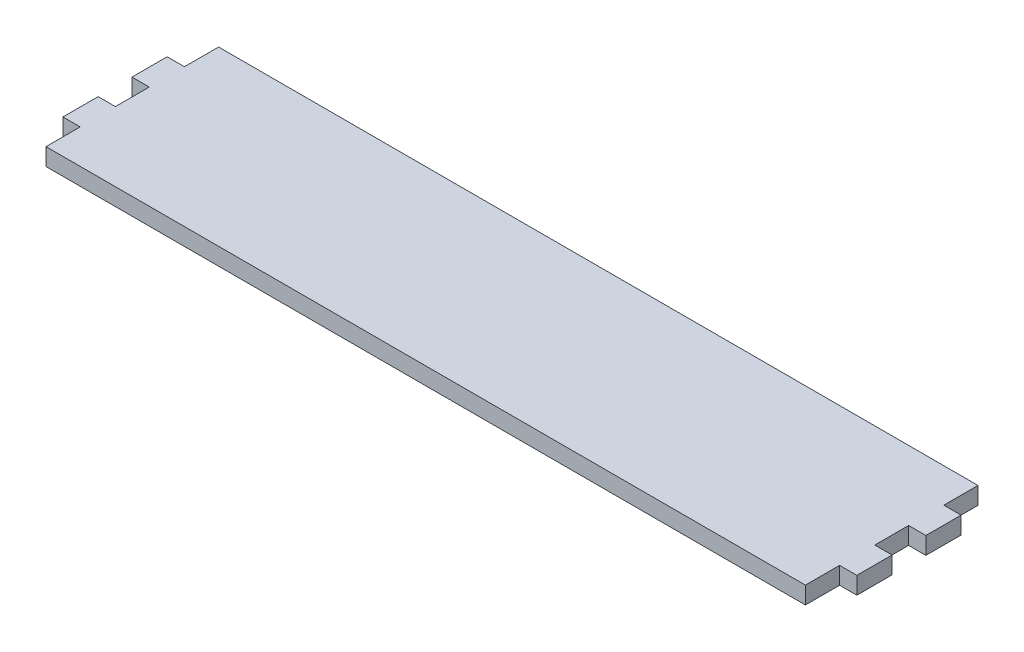
SolidWorks part; units mm, degrees
ref_plane "Front Plane" through (0, 0, 0) normal (0, 0, 1) x (1, 0, 0)
ref_plane "Top Plane" through (0, 0, 0) normal (0, 1, 0) x (1, 0, 0)
ref_plane "Right Plane" through (0, 0, 0) normal (1, 0, 0) x (0, 0, -1)
sketch "Sketch1" plane through (0, 0, 0) normal (0, 1, 0) x (1, 0, 0)
  line L0 (0, 0) -> (279.4, 0)
  line L1 (279.4, 0) -> (279.4, -12.573)
  line L2 (279.4, -12.573) -> (285.75, -12.573)
  line L3 (285.75, -12.573) -> (285.75, -25.527)
  line L4 (285.75, -25.527) -> (279.4, -25.527)
  line L5 (279.4, -25.527) -> (279.4, -37.973)
  line L6 (279.4, -37.973) -> (285.75, -37.973)
  line L7 (285.75, -37.973) -> (285.75, -50.927)
  line L8 (285.75, -50.927) -> (279.4, -50.927)
  line L9 (279.4, -50.927) -> (279.4, -63.5)
  line L10 (279.4, -63.5) -> (0, -63.5)
  line L11 (0, -63.5) -> (0, -50.927)
  line L12 (0, -50.927) -> (-6.35, -50.927)
  line L13 (-6.35, -50.927) -> (-6.35, -37.973)
  line L14 (-6.35, -37.973) -> (0, -37.973)
  line L15 (0, -37.973) -> (0, -25.527)
  line L16 (0, -25.527) -> (-6.35, -25.527)
  line L17 (-6.35, -25.527) -> (-6.35, -12.573)
  line L18 (-6.35, -12.573) -> (0, -12.573)
  line L19 (0, -12.573) -> (0, 0)
  dimension "D1" = 279.4
  dimension "D2" = 6.35
  dimension "D3" = 6.35
  dimension "D4" = 12.954
  dimension "D5" = 12.954
  dimension "D6" = 12.573
  dimension "D7" = 12.573
  dimension "D8" = 12.446
  dimension "D9" = 12.573
  dimension "D10" = 12.954
  dimension "D11" = 12.446
  dimension "D12" = 12.954
  dimension "D13" = 6.35
  dimension "D14" = 6.35
  dimension "D15" = 279.4
  dimension "D16" = 6.35
extrude "Boss-Extrude1" add sketch "Sketch1" along normal blind 6.35
